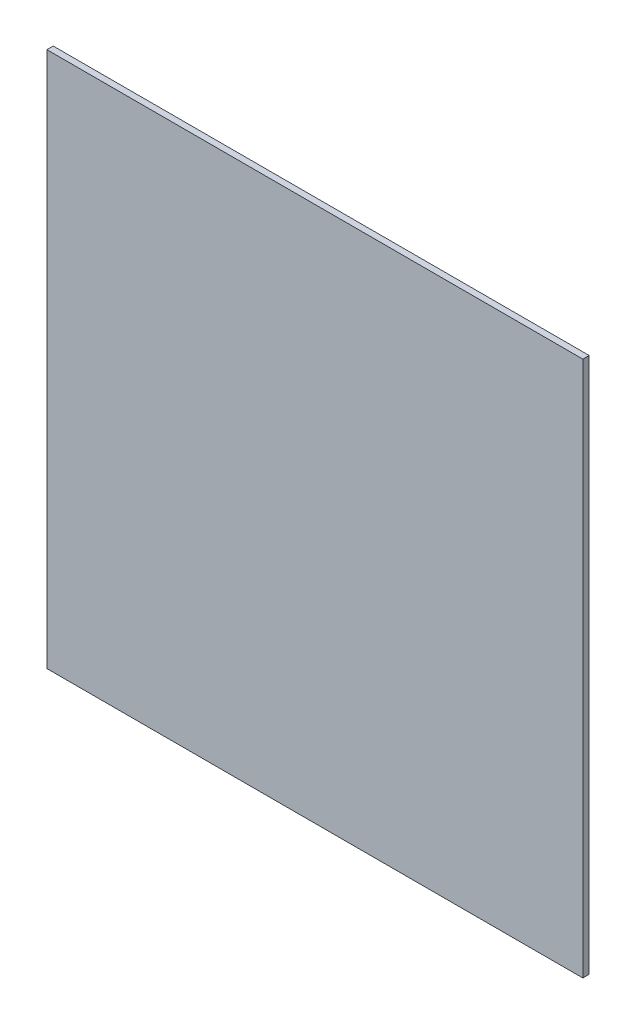
SolidWorks part; units mm, degrees
ref_plane "Front Plane" through (0, 0, 0) normal (0, 0, 1) x (1, 0, 0)
ref_plane "Top Plane" through (0, 0, 0) normal (0, 1, 0) x (1, 0, 0)
ref_plane "Right Plane" through (0, 0, 0) normal (1, 0, 0) x (0, 0, -1)
ref_plane "Plane1" through (0, 0, 3) normal (0, 0, 1) x (1, 0, 0)
sketch "Sketch1" plane through (0, 0, 3) normal (0, 0, 1) x (1, 0, 0)
  line L0 (127, 127) -> (-127, 127)
  line L1 (-127, 127) -> (-127, -127)
  line L2 (-127, -127) -> (127, -127)
  line L3 (127, -127) -> (127, 127)
  dimension "D1" = 254
  dimension "D2" = 254
extrude "Boss-Extrude1" add sketch "Sketch1" against normal blind 3
